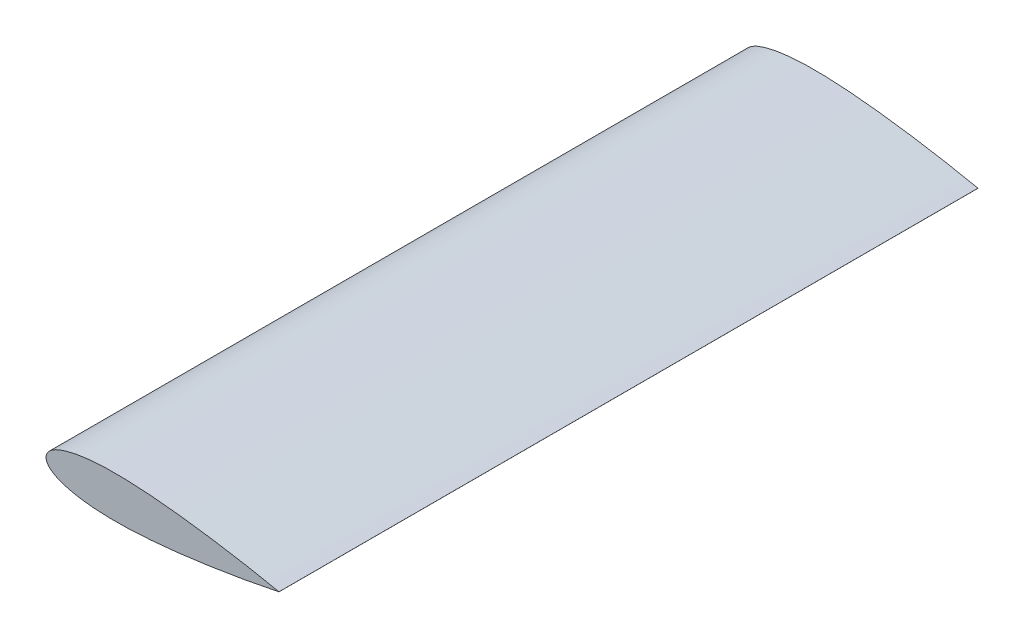
SolidWorks part; units mm, degrees
material "polystirene foam"
ref_plane "Front Plane" through (0, 0, 0) normal (0, 0, 1) x (1, 0, 0)
ref_plane "Top Plane" through (0, 0, 0) normal (0, 1, 0) x (1, 0, 0)
ref_plane "Right Plane" through (0, 0, 0) normal (1, 0, 0) x (0, 0, -1)
curve "Curve1"
  spline degree 3 poles (267.933, 0.5337, 0) (270.49, -0.1564, 0) (268.2375, 0.6665, 0) (266.5672, 1.4668, 0) (262.6756, 3.0154, 0) (257.9132, 4.5724, 0) (251.732, 6.3325, 0) (244.4112, 8.2376, 0) (235.9576, 10.2728, 0) (226.5142, 12.3893, 0) (216.1934, 14.5409, 0) (205.1313, 16.6775, 0) (193.4567, 18.7298, 0) (181.2977, 20.6324, 0) (168.7678, 22.3117, 0) (155.9753, 23.7079, 0) (143.0353, 24.8049, 0) (130.0617, 25.5802, 0) (117.1734, 26.0003, 0) (104.4837, 26.0576, 0) (92.1044, 25.7531, 0) (80.1395, 25.0742, 0) (68.69, 24.0381, 0) (57.8509, 22.6699, 0) (47.7143, 21.0125, 0) (38.3732, 19.0872, 0) (29.9084, 16.9558, 0) (22.399, 14.6444, 0) (15.9079, 12.2159, 0) (10.4843, 9.7202, 0) (6.177, 7.2209, 0) (2.9612, 4.7412, 0) (0.9766, 2.4261, 0) (0.0237, 0.7907, 0) (-0.0162, -0.4697, 0) (0.8003, -1.8361, 0) (3.4921, -2.6295, 0) (7.308, -3.6627, 0) (12.6566, -4.3991, 0) (19.3194, -5.0329, 0) (27.2905, -5.4698, 0) (36.4622, -5.7387, 0) (46.7414, -5.84, 0) (58.0105, -5.7702, 0) (70.1434, -5.5368, 0) (83.0071, -5.1408, 0) (96.4629, -4.5659, 0) (110.374, -3.827, 0) (124.6167, -2.893, 0) (139.0995, -1.7363, 0) (153.7348, -0.4008, 0) (168.4097, 0.8923, 0) (182.9339, 2.0414, 0) (197.0782, 2.9592, 0) (210.6044, 3.579, 0) (223.2667, 3.8744, 0) (234.8405, 3.8186, 0) (245.0477, 3.4533, 0) (253.7786, 2.7629, 0) (260.4407, 1.9422, 0) (265.7815, 0.9299, 0) (267.933, 0.5337, 0) (270.49, -0.1564, 0) (268.2375, 0.6665, 0) knots -0.016249 -0.007187 -0.001789 0 0.001694 0.006395 0.013462 0.022754 0.034367 0.048191 0.064031 0.081681 0.100894 0.121432 0.143025 0.165434 0.188439 0.211855 0.235496 0.259144 0.282615 0.305702 0.328232 0.35003 0.370944 0.390817 0.409506 0.426857 0.442733 0.457018 0.469615 0.48045 0.489472 0.49673 0.502329 0.506256 0.506442 0.509182 0.513914 0.521178 0.530944 0.543145 0.55767 0.574384 0.59311 0.613638 0.635744 0.659184 0.683714 0.709076 0.735036 0.76143 0.788184 0.815057 0.841645 0.867514 0.892232 0.915364 0.936485 0.9552 0.971104 0.983751 0.992813 0.998211 1 1.001694 1.006395 1.013462 periodic
curve "Curve2"
  spline degree 3 poles (1, 0.0019, 0) (0.9833, 0.0053, 0) (0.9501, 0.0122, 0) (0.8834, 0.025, 0) (0.8002, 0.0397, 0) (0.7001, 0.0553, 0) (0.6002, 0.0688, 0) (0.5002, 0.0799, 0) (0.4001, 0.0878, 0) (0.3167, 0.0906, 0) (0.25, 0.0895, 0) (0.1999, 0.0865, 0) (0.1497, 0.0808, 0) (0.1079, 0.0728, 0) (0.0746, 0.0633, 0) (0.0492, 0.0537, 0) (0.0279, 0.0421, 0) (0.0083, 0.0261, 0) (-0.0054, 0, 0) (0.0083, -0.0261, 0) (0.0279, -0.0421, 0) (0.0492, -0.0537, 0) (0.0746, -0.0633, 0) (0.1079, -0.0728, 0) (0.1497, -0.0808, 0) (0.1999, -0.0865, 0) (0.25, -0.0895, 0) (0.3167, -0.0906, 0) (0.4001, -0.0878, 0) (0.5002, -0.0799, 0) (0.6002, -0.0688, 0) (0.7001, -0.0553, 0) (0.8002, -0.0397, 0) (0.8834, -0.025, 0) (0.9501, -0.0122, 0) (0.9833, -0.0053, 0) (1, -0.0019, 0) knots 0 0 0 0 0.024604 0.049152 0.098109 0.146905 0.195555 0.244056 0.29241 0.340644 0.364754 0.388906 0.413178 0.437756 0.450305 0.46323 0.477068 0.485036 0.5 0.514964 0.522932 0.53677 0.549695 0.562244 0.586822 0.611094 0.635246 0.659356 0.70759 0.755944 0.804445 0.853095 0.901891 0.950848 0.975396 1 1 1 1
sketch "Sketch2" plane through (0, 0, 0) normal (0, 0, 1) x (1, 0, 0)
  line L1 (0, 0) -> (200, 0) construction
  line L2 (0, 5.3617) -> (0, 0) construction
  line L3 (200, 0.026) -> (200, -0.026)
  line L4 (0, 17.8541) -> (200, 17.8541) construction
  line L5 (0, -17.8541) -> (200, -17.8541) construction
  spline S1 degree 3 poles (200, 0.026) (196.1337, 0.8245) (188.9731, 2.314) (175.1972, 4.9535) (158.6821, 7.8644) (138.8483, 10.963) (119.0176, 13.6524) (99.1866, 15.8519) (79.3508, 17.4108) (62.8016, 17.9646) (49.5701, 17.7436) (39.6384, 17.1555) (29.688, 16.02) (21.4064, 14.4333) (14.8011, 12.5462) (9.7569, 10.6396) (5.5318, 8.3438) (1.6454, 5.1683) (-1.0737, 0) (1.6454, -5.1683) (5.5318, -8.3438) (9.7569, -10.6396) (14.8011, -12.5462) (21.4064, -14.4333) (29.688, -16.02) (39.6384, -17.1555) (49.5701, -17.7436) (62.8016, -17.9646) (79.3508, -17.4108) (99.1866, -15.8519) (119.0176, -13.6524) (138.8483, -10.963) (158.6821, -7.8644) (175.1972, -4.9535) (188.9731, -2.314) (196.1337, -0.8245) (200, -0.026) knots -0.00419 -0.00419 -0.00419 -0.00419 0.024604 0.049152 0.098109 0.146905 0.195555 0.244056 0.29241 0.340644 0.364754 0.388906 0.413178 0.437756 0.450305 0.46323 0.477068 0.485036 0.5 0.514964 0.522932 0.53677 0.549695 0.562244 0.586822 0.611094 0.635246 0.659356 0.70759 0.755944 0.804445 0.853095 0.901891 0.950848 0.975396 1.00419 1.00419 1.00419 1.00419
  dimension "D1" = 200
extrude "Boss-Extrude1" add sketch "Sketch2" along normal blind 600 contours S1 L3
